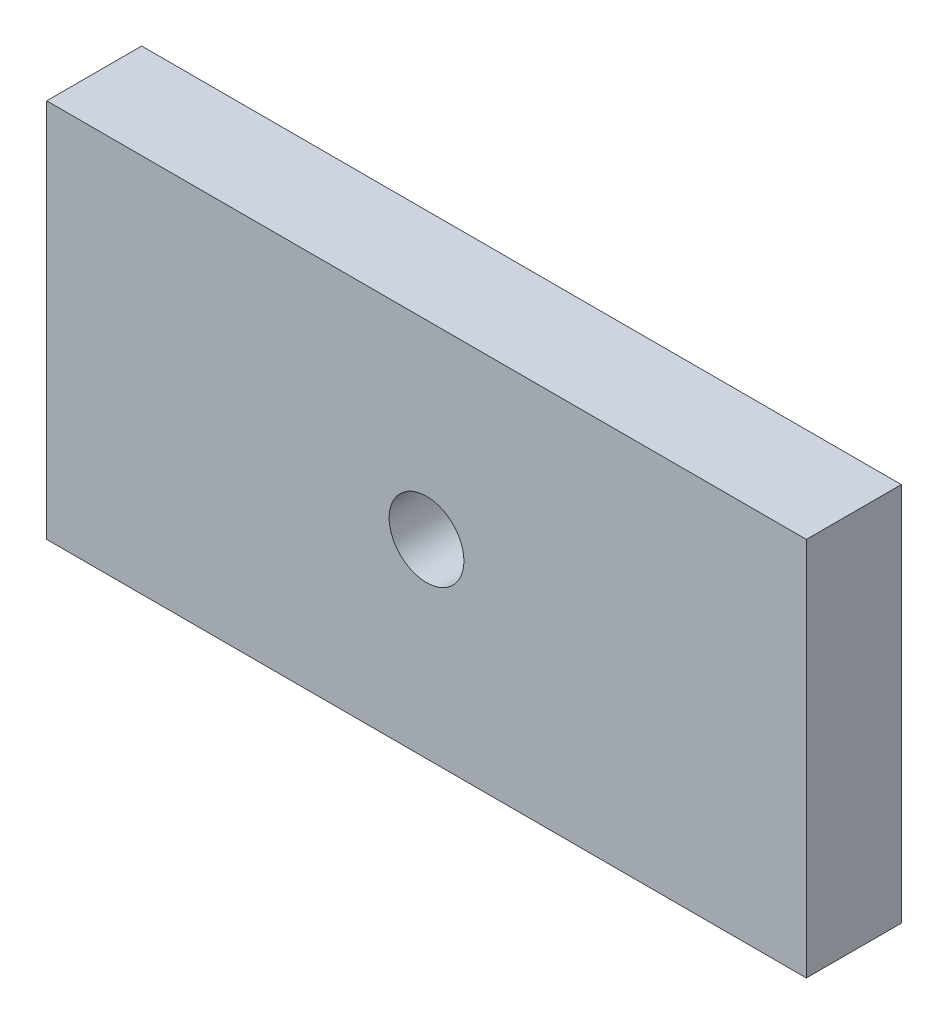
SolidWorks part; units mm, degrees
ref_plane "Front Plane" through (0, 0, 0) normal (0, 0, 1) x (1, 0, 0)
ref_plane "Top Plane" through (0, 0, 0) normal (0, 1, 0) x (1, 0, 0)
ref_plane "Right Plane" through (0, 0, 0) normal (1, 0, 0) x (0, 0, -1)
sketch "Sketch1" plane through (0, 0, 0) normal (0, 0, 1) x (1, 0, 0)
  line L1 (0, 0) -> (76.2, 0)
  line L2 (0, 0) -> (0, -38.1)
  line L3 (0, -38.1) -> (76.2, -38.1)
  line L4 (76.2, 0) -> (76.2, -38.1)
  line L5 (24.1, -5.05) -> (52.1, -5.05)
  line L6 (24.1, -5.05) -> (24.1, -33.05)
  line L7 (24.1, -33.05) -> (52.1, -33.05)
  line L8 (52.1, -5.05) -> (52.1, -33.05)
  circle A0 centre (38.1, -19.05) radius 3.75
  point P11 (38.1, -5.05)
  point P12 (52.1, -19.05)
  point P13 (36.1292, -18.2066)
  point P14 (0, 0)
  point P15 (0, -19.05)
  point P16 (0, 0)
  point P17 (38.1, 0)
  dimension "D5" = 7.5
  dimension "D1" = 28
  dimension "D2" = 28
  dimension "D3" = 76.2
  dimension "D4" = 38.1
extrude "Boss-Extrude1" add sketch "Sketch1" along normal blind 9.525 contours L4 L1 L2 L3 L5 L8 L7 L6 | L8 L5 L6 L7 A0
